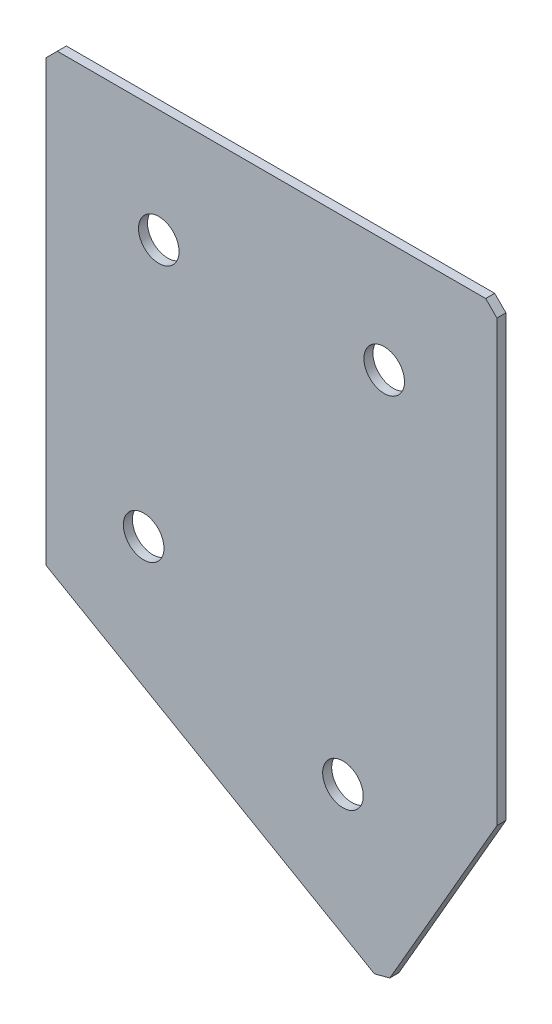
SolidWorks part; units mm, degrees
material "Простая углеродистая сталь"
ref_plane "Спереди" through (0, 0, 0) normal (0, 0, 1) x (1, 0, 0)
ref_plane "Сверху" through (0, 0, 0) normal (0, 1, 0) x (1, 0, 0)
ref_plane "Справа" through (0, 0, 0) normal (1, 0, 0) x (0, 0, -1)
sketch "Эскиз3" plane through (0, 0, 0) normal (0, 0, -1) x (1, 0, 0)
  line L0 (0, 0) -> (100, 0)
  line L1 (100, 0) -> (100, 100)
  line L2 (0, 0) -> (0, 100)
  line L3 (0, 100) -> (75, 143.3013)
  line L4 (75, 143.3013) -> (100, 100)
  dimension "D1" = 100
  dimension "D2" = 100
  dimension "D3" = 50
  dimension "D4" = 30
  dimension "D5" = 100
extrude "Бобышка-Вытянуть1" add sketch "Эскиз3" along normal blind 2
hole_wizard "Отверстие с зазором M81" positions "Эскиз4" profile "Эскиз5" hole size "M8" standard "DIN" end condition through all
sketch "Эскиз4" plane through (0, 0, -2) normal (0, 0, -1) x (1, 0, 0)
  line L0 (21.6506, 83.6325) -> (65.8494, 109.1506) construction
  line L2 (75, 143.3013) -> (0, 100) construction
  line L3 (25, 25) -> (75, 25) construction
  line L5 (0, 0) -> (100, 0) construction
  line L6 (0, 100) -> (0, 0) construction
  line L7 (100, 0) -> (100, 100) construction
  line L8 (100, 100) -> (75, 143.3013) construction
  line L9 (21.6506, 83.6325) -> (0, 71.1325) construction
  point P0 (25, 25)
  point P2 (75, 25)
  point P4 (21.6506, 83.6325)
  point P6 (65.8494, 109.1506)
  dimension "D1" = 25
  dimension "D2" = 25
  dimension "D3" = 25
  dimension "D4" = 25
  dimension "D5" = 25
  dimension "D6" = 25
  dimension "D7" = 51.0363
  dimension "D8" = 50
sketch "Эскиз5" plane through (25, -25, -2) normal (1, 0, 0) x (0, 1, 0)
  line L0 (0, 0) -> (0, 2)
  line L1 (0, 2) -> (4.5, 2)
  line L2 (4.5, 2) -> (4.5, 0)
  line L5 (4.5, 0) -> (0, 0)
  line L11 (0, -6.35) -> (0, 107.95) construction
  dimension "Диаметр сквозного отверстия" = 9
  dimension "Глубина сквозного отверстия" = 2
chamfer "Фаска1" distance 2.5 distance2 2.5 3 edges at (75, -143.3013, -1) (100, 0, -1) (0, 0, -1)
